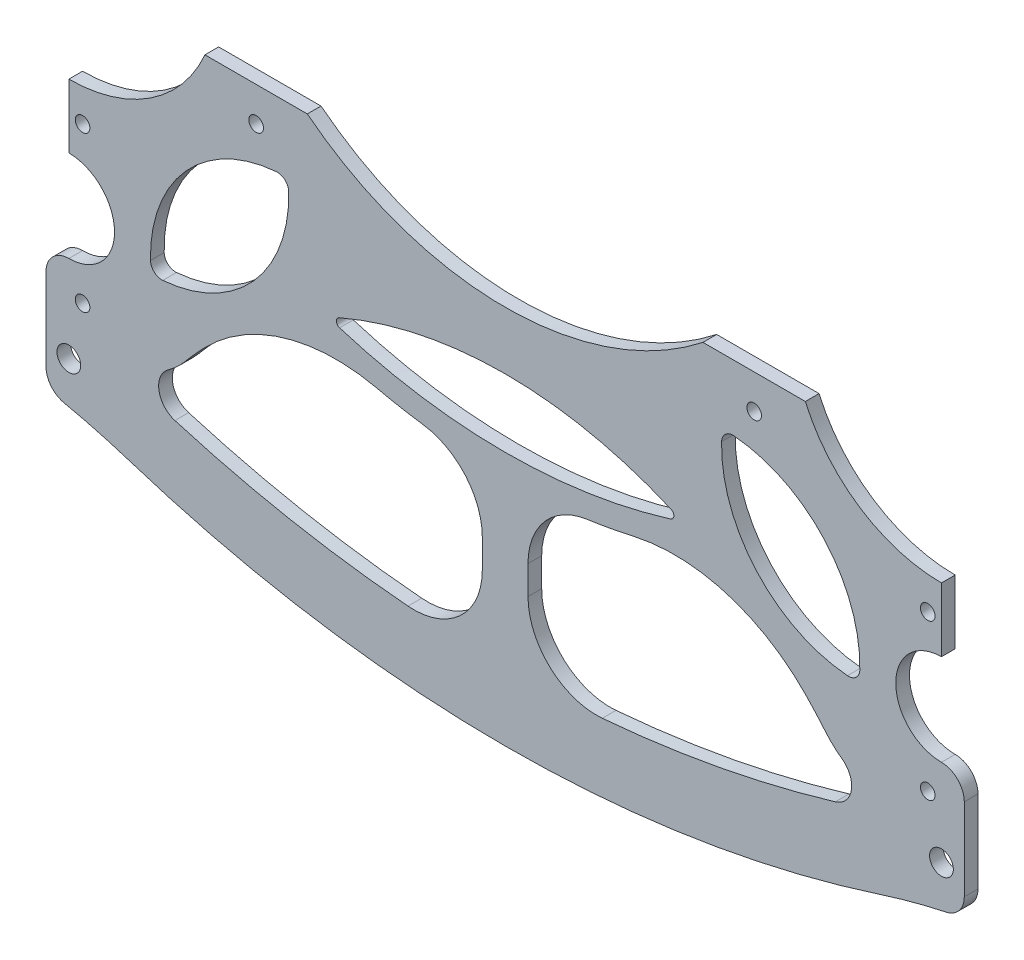
SolidWorks part; units mm, degrees
material "Thornel Mat VMA"
ref_plane "前视基准面" through (0, 0, 0) normal (0, 0, 1) x (1, 0, 0)
ref_plane "上视基准面" through (0, 0, 0) normal (0, 1, 0) x (1, 0, 0)
ref_plane "右视基准面" through (0, 0, 0) normal (1, 0, 0) x (0, 0, -1)
sketch "草图1" plane through (0, 0, 0) normal (0, 0, 1) x (1, 0, 0)
  line L0 (-95.5, -8.75) -> (95.5, -8.75) construction
  line L1 (-95.5, -33.75) -> (95.5, -33.75) construction
  line L2 (-95.5, -33.75) -> (-95.5, 33.75) construction
  line L3 (-95.5, 33.75) -> (95.5, 33.75) construction
  line L4 (95.5, -33.75) -> (95.5, 33.75) construction
  line L5 (-95.5, -33.75) -> (95.5, 33.75) construction
  line L6 (-95.5, 33.75) -> (95.5, -33.75) construction
  line L7 (-50, -8.75) -> (-50, -33.75) construction
  line L8 (50, -8.75) -> (50, -33.75) construction
  line L9 (-43.3013, 33.75) -> (-65.7133, 33.75)
  line L10 (-95.5, 14.25) -> (-95.5, 0.25)
  line L11 (-95.5, -19.75) -> (-95.5, -33.75)
  line L12 (-95.5, -33.75) -> (-75.5, -33.75)
  line L13 (0, 0) -> (0, -75.6259) construction
  line L14 (43.3013, 33.75) -> (65.7133, 33.75)
  line L15 (95.5, 14.25) -> (95.5, 0.25)
  line L16 (95.5, -19.75) -> (95.5, -33.75)
  line L17 (95.5, -33.75) -> (75.5, -33.75)
  circle A0 centre (0, -85.255) radius 91.3948 construction
  arc A1 (-75.5, -33.75) -> (75.5, -33.75) centre (0, -85.255) cw
  circle A2 centre (-95.5, -9.75) radius 10 construction
  circle A3 centre (-95.5, 46.75) radius 32.5 construction
  arc A4 (-95.5, -19.75) -> (-95.5, 0.25) centre (-95.5, -9.75) ccw
  arc A5 (-95.5, 14.25) -> (-65.7133, 33.75) centre (-95.5, 46.75) ccw
  arc A6 (95.5, -19.75) -> (95.5, 0.25) centre (95.5, -9.75) cw
  arc A7 (95.5, 14.25) -> (65.7133, 33.75) centre (95.5, 46.75) cw
  arc A8 (-43.3013, 33.75) -> (43.3013, 33.75) centre (0, 88.75) ccw
  point P0 (0, 0)
  point P12 (-75.5, -33.75)
  point P13 (75.5, -33.75)
  point P18 (-95.5, -9.75)
  point P21 (-95.5, 14.25)
  dimension "D8" = 24
  dimension "D9" = 20
  dimension "D11" = 65
  dimension "D12" = 140
  dimension "D1" = 67.5
  dimension "D2" = 191
  dimension "D3" = 25
  dimension "D4" = 50
  dimension "D5" = 50
  dimension "D6" = 20
  dimension "D7" = 20
  dimension "D10" = 48
  dimension "D13" = 55
extrude "凸台-拉伸1" add sketch "草图1" along normal blind 3 contours A8 L9 A5 L10 A4 L11 L12 A1 L17 L16 A6 L15 A7 L14
sketch "草图2" plane through (0, 0, 3) normal (0, 0, 1) x (1, 0, 0)
  line L0 (-43.3013, 33.75) -> (43.3013, 33.75) construction
  line L1 (0, 33.75) -> (0, -10.6023) construction
  line L2 (0, 33.75) -> (0, 113.75) construction
  circle A0 centre (0, 113.75) radius 125 construction
  arc A1 (-71.6448, 11.3194) -> (73.2747, 12.479) centre (0, 113.75) ccw
  dimension "D2" = 250
  dimension "D1" = 80
extrude "拉伸-薄壁1" add sketch "草图2" against normal up to surface (3 mm away) thin up to face at (0, 0.3934, 0) thin type mid plane wall 5
fillet "圆角1" radius 40 2 edges at (44.8284, -5.6094, 1.5) (-44.8284, -5.6094, 1.5)
sketch "草图3" plane through (0, 0, 3) normal (0, 0, 1) x (1, 0, 0)
  line L0 (-95.5, -33.75) -> (-29.5046, 39.5453) construction
  line L1 (-95.5, -33.75) -> (-75.5, -33.75) construction
  line L2 (0, 0) -> (0, 54.1854) construction
  line L3 (-62.5023, 2.8976) -> (-95.5, 32.6089) construction
  arc A0 (-77.4645, -13.7196) -> (-47.5401, 19.5149) centre (-77.3652, 16.2803) ccw
  arc A1 (-77.4645, -13.7196) -> (-47.5401, 19.5149) centre (-47.6394, -10.485) cw
  arc A2 (77.4645, -13.7196) -> (47.5401, 19.5149) centre (47.6394, -10.485) ccw
  arc A3 (77.4645, -13.7196) -> (47.5401, 19.5149) centre (77.3652, 16.2803) cw
  dimension "D2" = 60
  dimension "D1" = 20
  dimension "D3" = 98.6285
  dimension "D4" = 48
extrude "切除-拉伸1" cut sketch "草图3" against normal up to next
fillet "圆角2" radius 20 2 edges at (75.5, -33.75, 1.5) (-75.5, -33.75, 1.5)
sketch "草图4" plane through (0, 0, 3) normal (0, 0, 1) x (1, 0, 0)
  line L0 (-92.5, -33.75) -> (-92.5, -26.75) construction
  line L1 (-95.5, -33.75) -> (-85.4157, -33.75) construction
  line L2 (-95.5, -19.75) -> (-95.5, -33.75) construction
  line L3 (-92.5, -26.75) -> (-92.5, 7.25) construction
  line L5 (0, 0) -> (0, -52.8103) construction
  line L6 (92.5, -26.75) -> (92.5, 7.25) construction
  line L7 (92.5, -33.75) -> (92.5, -26.75) construction
  circle A0 centre (-92.5, -26.75) radius 1.6
  circle A1 centre (-92.5, 7.25) radius 1.6
  circle A2 centre (92.5, 7.25) radius 1.6
  circle A3 centre (92.5, -26.75) radius 1.6
  dimension "D3" = 3.2
  dimension "D5" = 3.2
  dimension "D1" = 3
  dimension "D2" = 7
  dimension "D4" = 34
extrude "切除-拉伸2" cut sketch "草图4" against normal up to next
sketch "草图5" plane through (0, 0, 3) normal (0, 0, 1) x (1, 0, 0)
  line L0 (-54.5073, 33.75) -> (-54.5073, 26.25) construction
  line L1 (-43.3013, 33.75) -> (-65.7133, 33.75) construction
  line L2 (0, 0) -> (0, 26.25) construction
  circle A0 centre (-54.5073, 26.25) radius 1.6
  circle A1 centre (54.5073, 26.25) radius 1.6
  dimension "D2" = 3.2
  dimension "D1" = 7.5
extrude "切除-拉伸3" cut sketch "草图5" against normal up to next
fillet "圆角3" radius 1 2 edges at (38.7228, -2.4688, 1.5) (-38.7228, -2.4688, 1.5)
sketch "草图6" plane through (0, 0, 3) normal (0, 0, 1) x (1, 0, 0)
  line L0 (-95.5, -24.75) -> (-95.5, -42.75) construction
  line L1 (-90.5, -24.75) -> (-90.5, -42.75)
  line L2 (-100.5, -24.75) -> (-100.5, -42.75)
  line L3 (0, 0) -> (0, -67.3999) construction
  line L4 (95.5, -24.75) -> (95.5, -42.75) construction
  line L5 (90.5, -24.75) -> (90.5, -42.75)
  line L6 (100.5, -24.75) -> (100.5, -42.75)
  arc A0 (-90.5, -24.75) -> (-100.5, -24.75) centre (-95.5, -24.75) ccw
  arc A1 (-100.5, -42.75) -> (-90.5, -42.75) centre (-95.5, -42.75) ccw
  circle A2 centre (-92.5, -26.75) radius 1.6
  circle A5 centre (92.5, -26.75) radius 1.6
  arc A6 (90.5, -24.75) -> (100.5, -24.75) centre (95.5, -24.75) cw
  arc A7 (100.5, -42.75) -> (90.5, -42.75) centre (95.5, -42.75) cw
  circle A8 centre (-95.5, -38.75) radius 2.6
  circle A9 centre (95.5, -38.75) radius 2.6
  point P2 (-95.5, -33.75)
  point P18 (95.5, -33.75)
  dimension "D1" = 3.2
  dimension "D2" = 5.2
  dimension "D3" = 5
extrude "凸台-拉伸2" add sketch "草图6" against normal up to surface (3 mm away) up to face at (56.1073, 26.25, 0)
fillet "圆角4" radius 30 2 edges at (90.5, -33.75, 1.5) (-90.5, -33.75, 1.5)
fillet "圆角5" radius 2.5 4 edges at (-77.4645, -13.7196, 1.5) (-47.5401, 19.5149, 1.5) (77.4645, -13.7196, 1.5) (47.5401, 19.5149, 1.5)
sketch "草图7" plane through (0, 0, 0) normal (0, 0, -1) x (-1, 0, 0)
  circle A0 centre (0, 203.0759) radius 260 construction
  arc A1 (-95.5, -38.75) -> (92.9122, -39.756) centre (0, 203.0759) ccw
  point P0 (-95.5, -38.75)
  point P1 (95.5, -38.75)
  dimension "D1" = 520
extrude "拉伸-薄壁2" add sketch "草图7" against normal up to surface (3 mm away) thin up to face at (0, -12.6463, 3) thin type mid plane wall 15
sketch "草图8" plane through (0, 0, 0) normal (0, 0, -1) x (-1, 0, 0)
  line L0 (-96.455, -41.1683) -> (-94.545, -36.3317) construction
  circle A0 centre (-95.5, -38.75) radius 2.6
  circle A1 centre (95.5, -38.75) radius 2.6
  dimension "D1" = 5.2
  dimension "D2" = 5.2
extrude "切除-拉伸4" cut sketch "草图8" against normal up to next (3 mm away)
sketch "草图9" plane through (0, 0, 0) normal (0, 0, -1) x (-1, 0, 0)
  line L0 (0, -11.4974) -> (0, -58.6144)
extrude "拉伸-薄壁3" add sketch "草图9" against normal up to surface (3 mm away) thin up to face at (92.9, -38.75, 3) thin type mid plane wall 10
fillet "圆角6" radius 15 2 edges at (-5, -49.3746, 1.5) (5, -49.3746, 1.5)
fillet "圆角7" radius 15 2 edges at (-5, -13.6519, 1.5) (5, -13.6519, 1.5)
fillet "圆角8" radius 5 2 edges at (-82.8943, -35.4294, 1.5) (82.8943, -35.4294, 1.5)
fillet "圆角9" radius 145 2 edges at (-93.7825, -47.4458, 1.5) (93.7825, -47.4458, 1.5)
